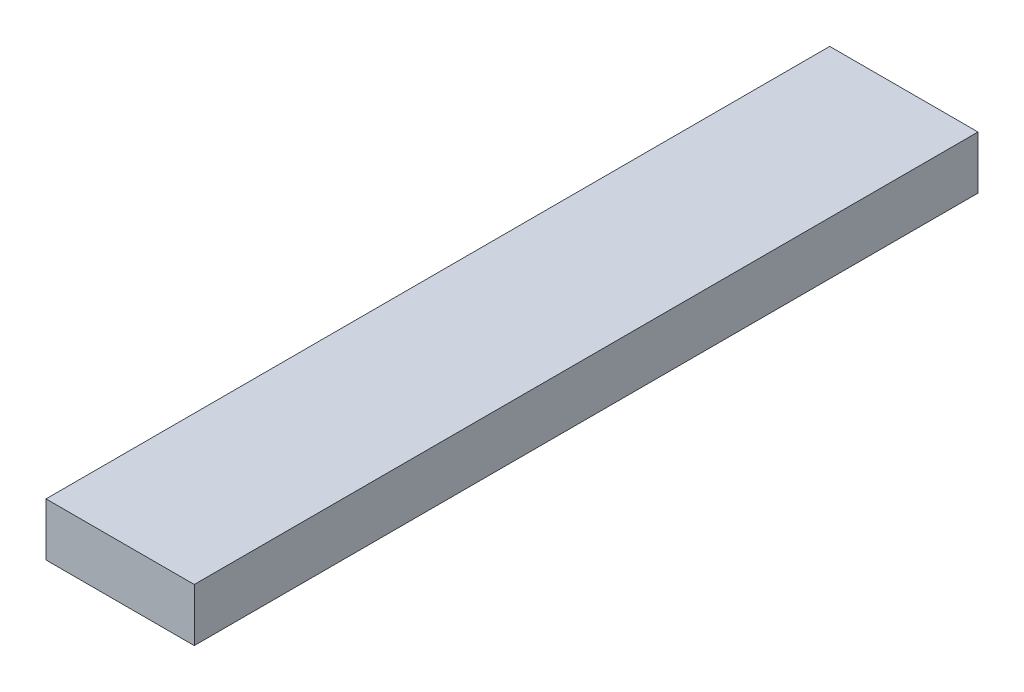
SolidWorks part; units mm, degrees
material "PVC 0.007 Plasticized"
ref_plane "Front Plane" through (0, 0, 0) normal (0, 0, 1) x (1, 0, 0)
ref_plane "Top Plane" through (0, 0, 0) normal (0, 1, 0) x (1, 0, 0)
ref_plane "Right Plane" through (0, 0, 0) normal (1, 0, 0) x (0, 0, -1)
sketch "Sketch1" plane through (0, 0, 0) normal (0, 1, 0) x (1, 0, 0)
  line L1 (0, 0) -> (14, 0)
  line L2 (0, 0) -> (0, 74)
  line L3 (0, 74) -> (14, 74)
  line L4 (14, 0) -> (14, 74)
  dimension "D1" = 14
  dimension "D2" = 74
extrude "Boss-Extrude1" add sketch "Sketch1" along normal blind 5
